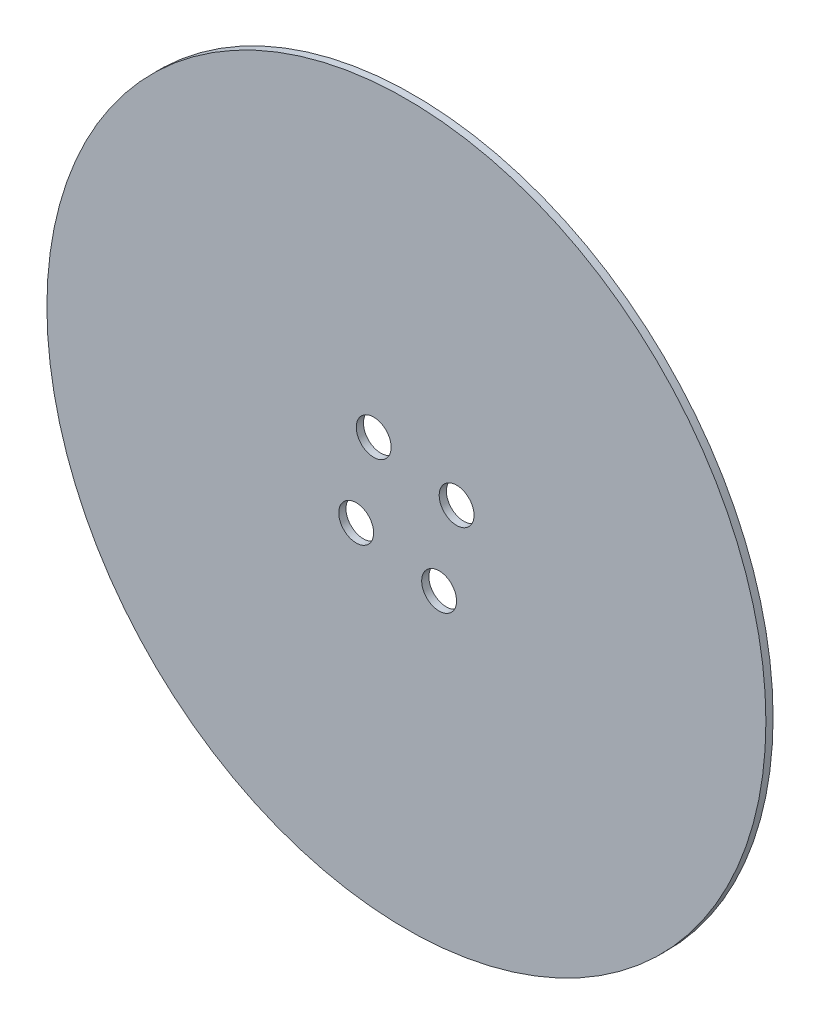
SolidWorks part; units mm, degrees
material "Acrylic (Medium-high impact)"
ref_plane "Front Plane" through (0, 0, 0) normal (0, 0, 1) x (1, 0, 0)
ref_plane "Top Plane" through (0, 0, 0) normal (0, 1, 0) x (1, 0, 0)
ref_plane "Right Plane" through (0, 0, 0) normal (1, 0, 0) x (0, 0, -1)
sketch "Sketch1" plane through (0, 0, 0) normal (0, 0, 1) x (1, 0, 0)
  line L0 (0, 0) -> (0, 140) construction
  line L1 (0, 140) -> (0, 150) construction
  line L2 (-12.5, 140) -> (12.5, 140) construction
  circle A0 centre (0, 0) radius 150
  point P9 (0, 140)
  point P21 (0, 0)
  dimension "D1" = 300
  dimension "D5" = 140
extrude "Boss-Extrude2" add sketch "Sketch1" along normal blind 3
sketch "Sketch2" plane through (0, 0, 0) normal (0, 0, -1) x (-1, 0, 0)
  circle A13 centre (-13.6439, -20.9486) radius 3.2 construction
  circle A14 centre (20.9486, -13.6439) radius 3.2 construction
  circle A15 centre (13.6439, 20.9486) radius 3.2 construction
  circle A16 centre (-20.9486, 13.6439) radius 3.2 construction
  circle A17 centre (-13.6439, -20.9486) radius 3.2
  circle A18 centre (20.9486, -13.6439) radius 3.2
  circle A19 centre (13.6439, 20.9486) radius 3.2
  circle A20 centre (-20.9486, 13.6439) radius 3.2
hole_wizard "CBORE for M6 Hex Head Bolt1" positions "Sketch8" profile "Sketch9" counterbore size "M6" standard "ANSI Metric" end condition through all
sketch "Sketch8" plane through (0, 0, 0) normal (0, 0, -1) x (-1, 0, 0)
  point P0 (-20.9486, 13.6439)
  point P3 (13.6439, 20.9486)
  point P6 (20.9486, -13.6439)
  point P9 (-13.6439, -20.9486)
sketch "Sketch9" plane through (20.9486, 13.6439, 0) normal (1, 0, 0) x (0, 1, 0)
  line L0 (0, 0) -> (0, 3)
  line L1 (0, 3) -> (3.3, 3)
  line L3 (3.3, 3) -> (3.3, 4.38)
  line L4 (3.3, 4.38) -> (7.275, 4.38)
  line L5 (7.275, 4.38) -> (7.275, 0)
  line L7 (7.275, 0) -> (0, 0)
  line L11 (0, -6.35) -> (0, 107.95) construction
  dimension "Thru Hole Dia." = 6.6
  dimension "Thru Hole Depth" = 3
  dimension "C'Bore Dia." = 14.55
  dimension "C'Bore Depth" = 4.38
